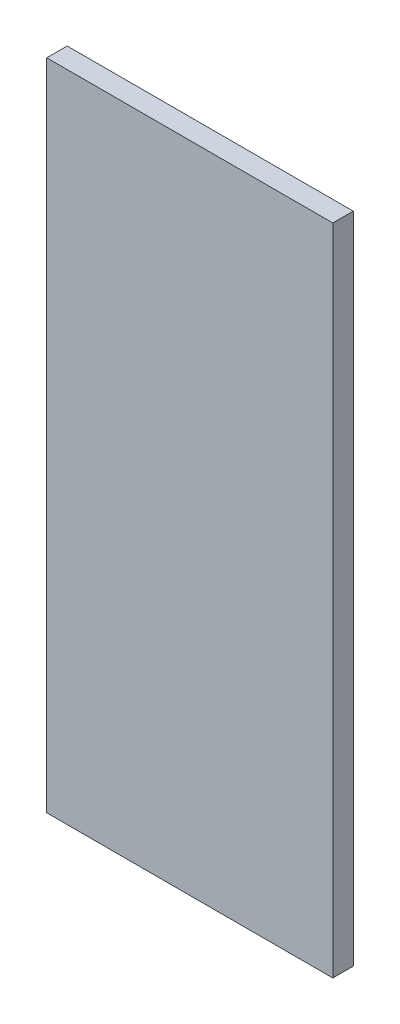
SolidWorks part; units mm, degrees
ref_plane "Front Plane" through (0, 0, 0) normal (0, 0, 1) x (1, 0, 0)
ref_plane "Top Plane" through (0, 0, 0) normal (0, 1, 0) x (1, 0, 0)
ref_plane "Right Plane" through (0, 0, 0) normal (1, 0, 0) x (0, 0, -1)
sketch "Sketch1" plane through (0, 0, 0) normal (0, 1, 0) x (1, 0, 0)
  line L1 (0, 0) -> (88.9, 0)
  line L2 (0, 0) -> (0, 6.35)
  line L3 (0, 6.35) -> (88.9, 6.35)
  line L4 (88.9, 0) -> (88.9, 6.35)
  dimension "D1" = 88.9
  dimension "D2" = 6.35
extrude "Boss-Extrude1" add sketch "Sketch1" along normal blind 203.2
ref_plane "Plane1" through (44.45, 0, 0) normal (-1, 0, 0) x (0, 0, 1)
